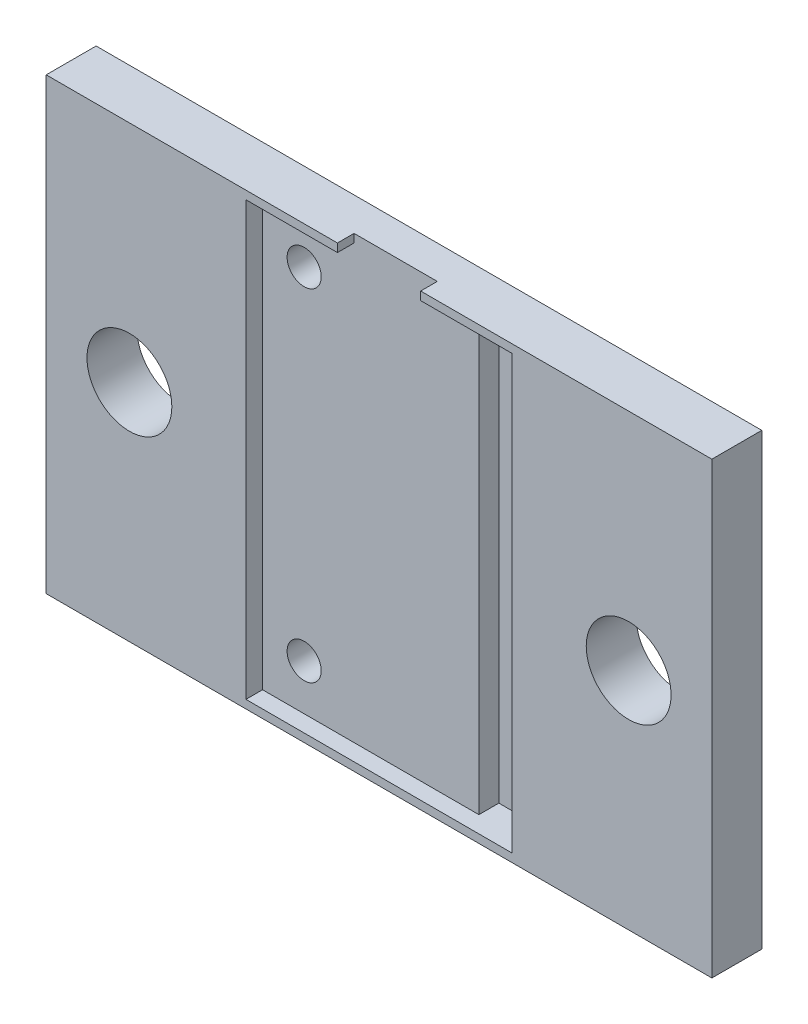
SolidWorks part; units mm, degrees
ref_plane "Front Plane" through (0, 0, 0) normal (0, 0, 1) x (1, 0, 0)
ref_plane "Top Plane" through (0, 0, 0) normal (0, 1, 0) x (1, 0, 0)
ref_plane "Right Plane" through (0, 0, 0) normal (1, 0, 0) x (0, 0, -1)
sketch "Sketch1" plane through (0, 0, 0) normal (0, 0, 1) x (1, 0, 0)
  line L0 (-7.5, 0) -> (7.5, 0) construction
  line L1 (-7.5, -12.5) -> (7.5, -12.5)
  line L2 (-7.5, -12.5) -> (-7.5, 12.5)
  line L3 (-7.5, 12.5) -> (7.5, 12.5)
  line L4 (7.5, -12.5) -> (7.5, 12.5)
  line L5 (-7.5, -12.5) -> (7.5, 12.5) construction
  line L6 (-7.5, 12.5) -> (7.5, -12.5) construction
  line L7 (6, 12.5) -> (6, -12.5) construction
  circle A0 centre (-5.5, 10.25) radius 1.5
  circle A1 centre (-5.5, -10.25) radius 1.5
  point P0 (0, 0)
  dimension "D3" = 3
  dimension "D1" = 15
  dimension "D2" = 25
  dimension "D4" = 2.25
  dimension "D5" = 2
  dimension "D6" = 1.5
sketch "Sketch3" plane through (0, 0, 0) normal (0, 0, 1) x (1, 0, 0)
  line L0 (-20, 0) -> (20, 0) construction
  line L5 (-20, -13.5) -> (20, -13.5)
  line L6 (-20, -13.5) -> (-20, 13.5)
  line L7 (-20, 13.5) -> (20, 13.5)
  line L8 (20, -13.5) -> (20, 13.5)
  line L9 (-20, -13.5) -> (20, 13.5) construction
  line L10 (-20, 13.5) -> (20, -13.5) construction
  line L11 (0, 13.5) -> (0, -13.5) construction
  circle A0 centre (-15, 0) radius 2.55
  circle A1 centre (15, 0) radius 2.55
  point P0 (0, 0)
  dimension "D3" = 5.1
  dimension "D1" = 27
  dimension "D2" = 40
  dimension "D4" = 5
extrude "Boss-Extrude1" add sketch "Sketch3" along normal blind 3
sketch "Sketch4" plane through (0, 0, 3) normal (0, 0, 1) x (1, 0, 0)
  line L0 (8, 13) -> (-8, 13) construction
  line L1 (-8, 13) -> (-8, -13)
  line L2 (-8, -13) -> (8, -13)
  line L3 (8, -13) -> (8, 13)
  line L4 (-7.5, -12.5) -> (7.5, -12.5)
  line L5 (7.5, -12.5) -> (7.5, 12.5)
  line L6 (7.5, 12.5) -> (-7.5, 12.5)
  line L7 (-7.5, 12.5) -> (-7.5, -12.5)
  line L8 (-7.5, -12.5) -> (7.5, -12.5) construction
  line L9 (7.5, -12.5) -> (7.5, 12.5) construction
  line L10 (7.5, 12.5) -> (-7.5, 12.5) construction
  line L11 (-7.5, 12.5) -> (-7.5, -12.5) construction
  line L12 (-2.5, 13) -> (-2.5, 13.5)
  line L13 (20, 13.5) -> (-20, 13.5) construction
  line L14 (-2.5, 13.5) -> (2.5, 13.5)
  line L15 (2.5, 13.5) -> (2.5, 13)
  line L16 (-8, 13) -> (-2.5, 13)
  line L17 (2.5, 13) -> (8, 13)
  line L18 (0, 0) -> (0, 13.5) construction
  circle A1 centre (-5.5, -10.25) radius 1.5
  circle A2 centre (-5.5, -10.25) radius 1.5 construction
  circle A3 centre (-5.5, 10.25) radius 1.5
  circle A4 centre (-5.5, 10.25) radius 1.5 construction
  point P23 (0, 13.5)
  dimension "D5" = 5
  dimension "D1" = 0
  dimension "D2" = 0
  dimension "D3" = 0
  dimension "D4" = 0.5
extrude "Cut-Extrude1" cut sketch "Sketch4" against normal blind 1
sketch "Sketch5" plane through (0, 0, 2) normal (0, 0, 1) x (1, 0, 0)
  line L0 (-8, -13) -> (8, -13) construction
  line L1 (5, -13) -> (8, -13)
  line L2 (5, -13) -> (5, 13)
  line L3 (5, 13) -> (8, 13)
  line L4 (8, -13) -> (8, 13)
  line L5 (5, -13) -> (8, 13) construction
  line L6 (5, 13) -> (8, -13) construction
  line L7 (8, 13) -> (2.5, 13) construction
  line L8 (8, -13) -> (8, 13) construction
  point P0 (6.5, 0)
  dimension "D1" = 3
extrude "Cut-Extrude2" cut sketch "Sketch5" against normal blind 1.2
sketch "Sketch6" plane through (0, 0, 2) normal (0, 0, 1) x (1, 0, 0)
  line L4 (-7.5, -12.5) -> (7.5, -12.5)
  line L5 (7.5, -12.5) -> (7.5, 12.5)
  line L6 (7.5, 12.5) -> (-7.5, 12.5)
  line L7 (-7.5, 12.5) -> (-7.5, -12.5)
  line L8 (-7.5, -12.5) -> (7.5, -12.5) construction
  line L9 (7.5, -12.5) -> (7.5, 12.5) construction
  line L10 (7.5, 12.5) -> (-7.5, 12.5) construction
  line L11 (-7.5, 12.5) -> (-7.5, -12.5) construction
  circle A0 centre (-5.5, 10.25) radius 1.025
  circle A1 centre (-5.5, -10.25) radius 1.5
  circle A2 centre (-5.5, -10.25) radius 1.5 construction
  circle A3 centre (-5.5, 10.25) radius 1.5
  circle A4 centre (-5.5, 10.25) radius 1.5 construction
  circle A5 centre (-5.5, -10.25) radius 1.025
  dimension "D4" = 2.05
  dimension "D5" = 2.05
  dimension "D1" = 0
  dimension "D2" = 0
  dimension "D3" = 0
extrude "Cut-Extrude3" cut sketch "Sketch6" against normal blind 3
